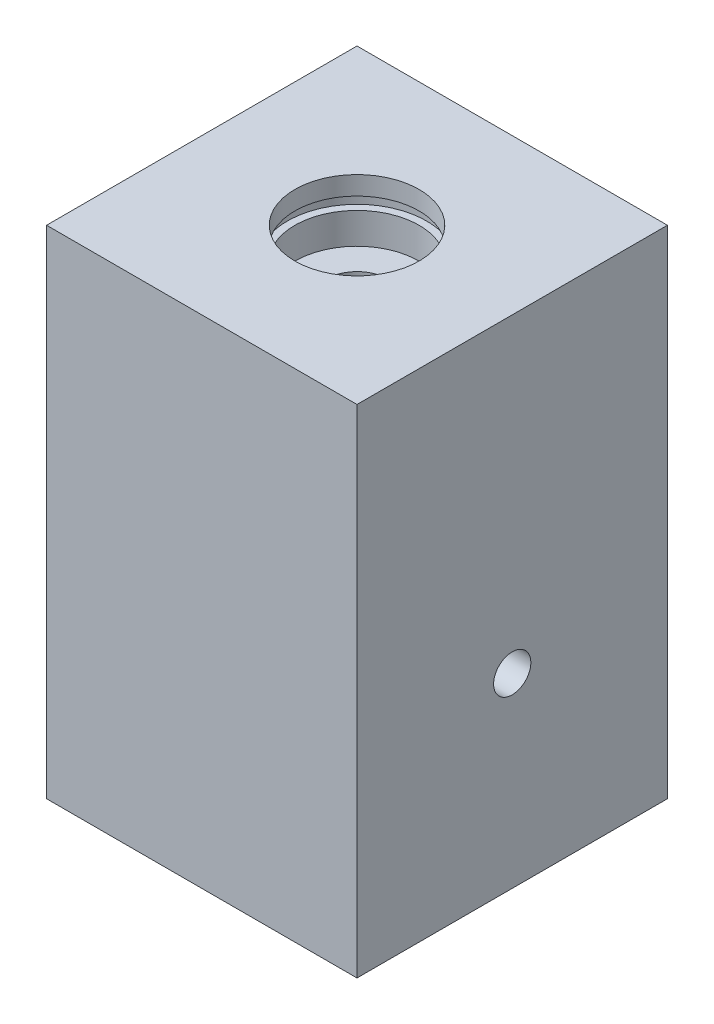
SolidWorks part; units mm, degrees
material "Rostfreier Chromstahl"
ref_plane "Ebene vorne" through (0, 0, 0) normal (0, 0, 1) x (1, 0, 0)
ref_plane "Ebene oben" through (0, 0, 0) normal (0, 1, 0) x (1, 0, 0)
ref_plane "Ebene rechts" through (0, 0, 0) normal (1, 0, 0) x (0, 0, -1)
sketch "Skizze1" plane through (0, 0, 0) normal (1, 0, 0) x (0, 0, -1)
  line L0 (0, 50) -> (0, -30) construction
  line L1 (0, 0) -> (25, 0) construction
  line L2 (-25, 50) -> (25, 50)
  line L3 (-25, 50) -> (-25, -30)
  line L4 (-25, -30) -> (25, -30)
  line L5 (25, 50) -> (25, -30)
  dimension "D1" = 50
  dimension "D2" = 30
  dimension "D3" = 50
extrude "Aufsatz-Linear austragen1" add sketch "Skizze1" along normal mid plane 50
sketch "Skizze2" plane through (0, 0, 0) normal (1, 0, 0) x (0, 0, -1)
  line L0 (0, 50) -> (0, -30) construction
  line L1 (0, 50) -> (0, -23.0043)
  line L2 (0, -23.0043) -> (5, -20)
  line L3 (5, -20) -> (5, 40)
  line L4 (5, 40) -> (10, 40)
  line L5 (10, 40) -> (10, 45)
  line L6 (-25, 50) -> (25, 50) construction
  line L7 (10, 50) -> (0, 50)
  line L8 (0, -23.0043) -> (0, -30) construction
  line L9 (-25, -30) -> (25, -30) construction
  line L10 (0, 0) -> (25, 0) construction
  line L11 (10, 47) -> (11.2, 47)
  line L12 (11.2, 47) -> (11.2, 45)
  line L13 (11.2, 45) -> (10, 45)
  line L14 (10, 47) -> (10, 50)
  dimension "D1" = 10
  dimension "D2" = 10
  dimension "D3" = 20
  dimension "D4" = 20
  dimension "D5" = 59
  dimension "D6" = 1.2
  dimension "D7" = 2
  dimension "D8" = 3
revolve "Schnitt-Rotation1" cut sketch "Skizze2" angle 360 about L8
hole_wizard "Ø6.0 (6) Durchmesser Bohrung1" positions "Skizze3" profile "Skizze4" hole size "Ø6.0" standard "DIN" end condition through all
sketch "Skizze3" plane through (25, 0, 0) normal (1, 0, 0) x (0, 0, -1)
  point P0 (0, 0)
  point P3 (0, 0)
sketch "Skizze4" plane through (25, 0, 0) normal (0, 1, 0) x (0, 0, -1)
  line L0 (0, 0) -> (0, 50)
  line L1 (0, 50) -> (3, 50)
  line L2 (3, 50) -> (3, 0)
  line L5 (3, 0) -> (0, 0)
  line L11 (0, -6.35) -> (0, 107.95) construction
  dimension "Bohrerdurchmesser" = 6
  dimension "Bohrungstiefe" = 50
